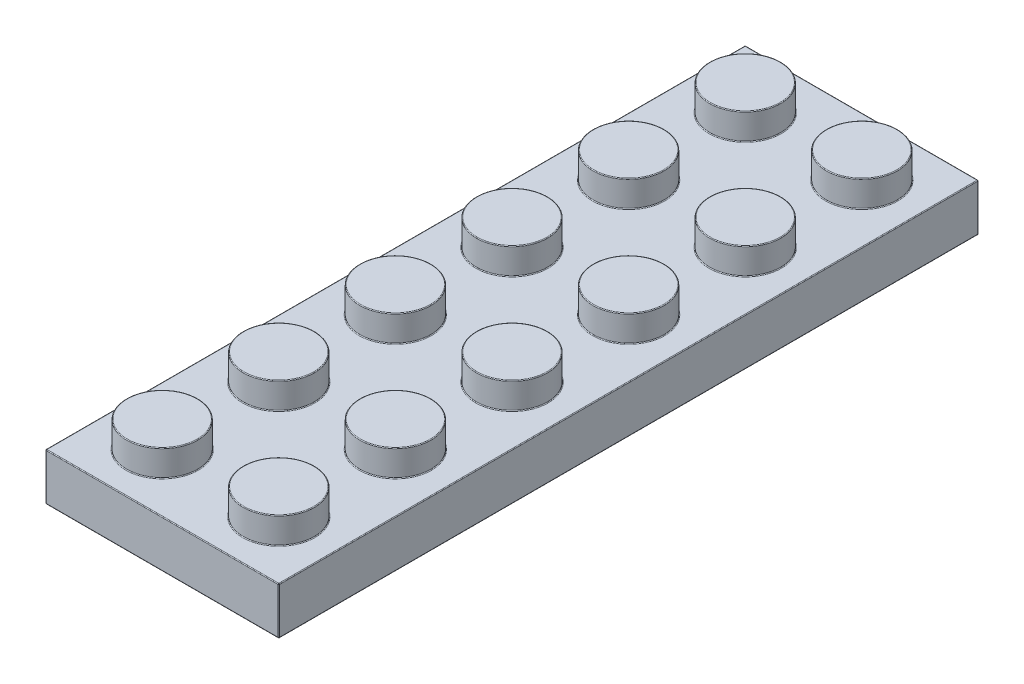
SolidWorks part; units mm, degrees
ref_plane "Front Plane" through (0, 0, 0) normal (0, 0, 1) x (1, 0, 0)
ref_plane "Top Plane" through (0, 0, 0) normal (0, 1, 0) x (1, 0, 0)
ref_plane "Right Plane" through (0, 0, 0) normal (1, 0, 0) x (0, 0, -1)
sketch "Sketch1" plane through (0, 0, 0) normal (0, 1, 0) x (1, 0, 0)
  line L1 (-3.98, 3.98) -> (3.98, 3.98)
  line L2 (-3.98, 3.98) -> (-3.98, -3.98)
  line L3 (-3.98, -3.98) -> (3.98, -3.98)
  line L4 (3.98, 3.98) -> (3.98, -3.98)
  line L5 (-3.98, 3.98) -> (3.98, -3.98) construction
  line L6 (-3.98, -3.98) -> (3.98, 3.98) construction
  point P0 (0, 0)
  dimension "D1" = 7.96
extrude "Extrude1" add sketch "Sketch1" along normal blind 3.22
sketch "Sketch2" plane through (0, 3.22, 0) normal (0, 1, 0) x (1, 0, 0)
  circle A0 centre (0, 0) radius 2.425
  dimension "D1" = 4.85
extrude "Extrude2" add sketch "Sketch2" along normal blind 1.8
pattern_linear "LPattern1" count 2 spacing 7.96 along (1, 0, 0) of "Extrude2", "Extrude1"
pattern_linear "LPattern2" count 6 spacing 7.96 along (0, 0, -1) of "LPattern1", "Extrude1", "Extrude2"
shell "Shell1" thickness 1.55
sketch "Sketch4" plane through (0, 1.67, 0) normal (0, -1, 0) x (1, 0, 0)
  line L0 (10.39, -42.23) -> (-2.43, -42.23) construction
  line L1 (-2.43, -42.23) -> (-2.43, 2.43) construction
  line L2 (-2.43, 2.43) -> (10.39, 2.43) construction
  line L3 (10.39, 2.43) -> (10.39, -42.23) construction
  line L4 (10.39, -42.23) -> (-2.43, -42.23)
  line L5 (-2.43, -42.23) -> (-2.43, 2.43)
  line L6 (-2.43, 2.43) -> (10.39, 2.43)
  line L7 (10.39, 2.43) -> (10.39, -42.23)
extrude "Extrude3" cut sketch "Sketch4" against normal blind 0.14
sketch "Sketch5" plane through (0, 1.81, 0) normal (0, -1, 0) x (1, 0, 0)
  line L0 (3.98, 2.43) -> (3.98, -42.23) construction
  line L1 (-2.43, 2.43) -> (10.39, 2.43) construction
  line L2 (-2.43, -42.23) -> (10.39, -42.23) construction
  line L3 (3.98, -35.82) -> (3.98, -27.86) construction
  line L4 (0, -31.84) -> (7.96, -31.84) construction
  line L5 (0, -31.84) -> (0, -39.8) construction
  line L6 (0, -39.8) -> (7.96, -39.8) construction
  line L7 (7.96, -31.84) -> (7.96, -39.8) construction
  line L8 (0, -23.88) -> (7.96, -23.88) construction
  line L9 (0, -23.88) -> (0, -31.84) construction
  line L10 (0, -31.84) -> (7.96, -31.84) construction
  line L11 (7.96, -23.88) -> (7.96, -31.84) construction
  line L12 (0, -15.92) -> (7.96, -15.92) construction
  line L13 (0, -15.92) -> (0, -23.88) construction
  line L14 (0, -23.88) -> (7.96, -23.88) construction
  line L15 (7.96, -15.92) -> (7.96, -23.88) construction
  line L16 (0, -7.96) -> (7.96, -7.96) construction
  line L17 (0, -7.96) -> (0, -15.92) construction
  line L18 (0, -15.92) -> (7.96, -15.92) construction
  line L19 (7.96, -7.96) -> (7.96, -15.92) construction
  line L20 (0, 0) -> (7.96, 0) construction
  line L21 (0, 0) -> (0, -7.96) construction
  line L22 (0, -7.96) -> (7.96, -7.96) construction
  line L23 (7.96, 0) -> (7.96, -7.96) construction
  circle A0 centre (3.98, -35.82) radius 3.23
  circle A1 centre (3.98, -35.82) radius 2.37
  circle A2 centre (3.98, -27.86) radius 3.23
  circle A3 centre (3.98, -27.86) radius 2.37
  circle A4 centre (3.98, -19.9) radius 3.23
  circle A5 centre (3.98, -19.9) radius 2.37
  circle A6 centre (3.98, -11.94) radius 3.23
  circle A7 centre (3.98, -11.94) radius 2.37
  circle A8 centre (3.98, -3.98) radius 3.23
  circle A9 centre (3.98, -3.98) radius 2.37
  point P27 (7.96, -35.82)
  point P28 (7.96, -27.86)
  dimension "D1" = 6.46
  dimension "D2" = 0.86
  dimension "D3" = 7.96
extrude "Extrude4" add sketch "Sketch5" along normal up to surface (1.81 mm away) up to face at (3.98, 0, -19.9)
fillet "Fillet1" radius 0.05 92 edges at (-3.98, 3.22, -19.9) (7.96, 3.22, -29.415) (7.96, 5.02, -29.415) (3.98, 0, -43.78) (11.94, 1.61, -43.78) (-3.98, 1.61, -43.78) (3.98, 3.22, -43.78) (0, 3.22, -37.375) (0, 5.02, -37.375) (7.96, 3.22, -37.375) (7.96, 5.02, -37.375) (-2.43, 0, -19.9) (-2.43, 0.905, -42.23) (3.98, 0, 2.43) (-2.43, 0.905, 2.43) (0, 3.47, 0.875) (10.39, 0, -19.9) (10.39, 0.905, 2.43) (7.96, 3.47, 0.875) (0, 3.47, -7.085) (3.98, 3.22, 3.98) (7.96, 3.47, -7.085) (0, 3.47, -15.045) (7.96, 3.47, -15.045) (0, 3.47, -23.005) (7.96, 3.47, -23.005) (0, 3.47, -30.965) (7.96, 3.47, -30.965) (3.98, 0, -42.23) (10.39, 0.905, -42.23) (0, 3.47, -38.925) (7.96, 3.47, -38.925) (0, 3.22, 2.425) (0, 5.02, 2.425) (0, 1.81, 0.875) (7.96, 1.81, 0.875) (0, 1.81, -7.085) (7.96, 1.81, -7.085) (0, 1.81, -15.045) (7.96, 1.81, -15.045) (0, 1.81, -23.005) (7.96, 1.81, -23.005) (0, 1.81, -30.965) (7.96, 1.81, -30.965) (0, 1.81, -38.925) (7.96, 1.81, -38.925) (10.39, 1.81, -19.9) (3.98, 1.81, -42.23) (-2.43, 1.81, -19.9) (3.98, 1.81, 2.43) (11.94, 0, -19.9) (11.94, 1.61, 3.98) (11.94, 3.22, -19.9) (3.98, 1.81, -32.59) (3.98, 1.81, -38.19) (3.98, 0, -32.59) (3.98, 0, -33.45) (3.98, 1.81, -24.63) (3.98, 1.81, -30.23) (3.98, 0, -24.63) (3.98, 0, -25.49) (3.98, 1.81, -16.67) (3.98, 1.81, -22.27) (3.98, 0, -16.67) (3.98, 0, -17.53) (3.98, 1.81, -8.71) (3.98, 1.81, -14.31) (3.98, 0, -8.71) (3.98, 0, -9.57) (3.98, 1.81, -0.75) (3.98, 1.81, -6.35) (3.98, 0, -0.75) (3.98, 0, -1.61) (7.96, 3.22, 2.425) (7.96, 5.02, 2.425) (3.98, 0, 3.98) (0, 3.22, -5.535) (0, 5.02, -5.535) (7.96, 3.22, -5.535) (7.96, 5.02, -5.535) (-3.98, 0, -19.9) (0, 3.22, -13.495) (0, 5.02, -13.495) (7.96, 3.22, -13.495) (7.96, 5.02, -13.495) (-3.98, 1.61, 3.98) (0, 3.22, -21.455) (0, 5.02, -21.455) (7.96, 3.22, -21.455) (7.96, 5.02, -21.455) (0, 3.22, -29.415) (0, 5.02, -29.415)
